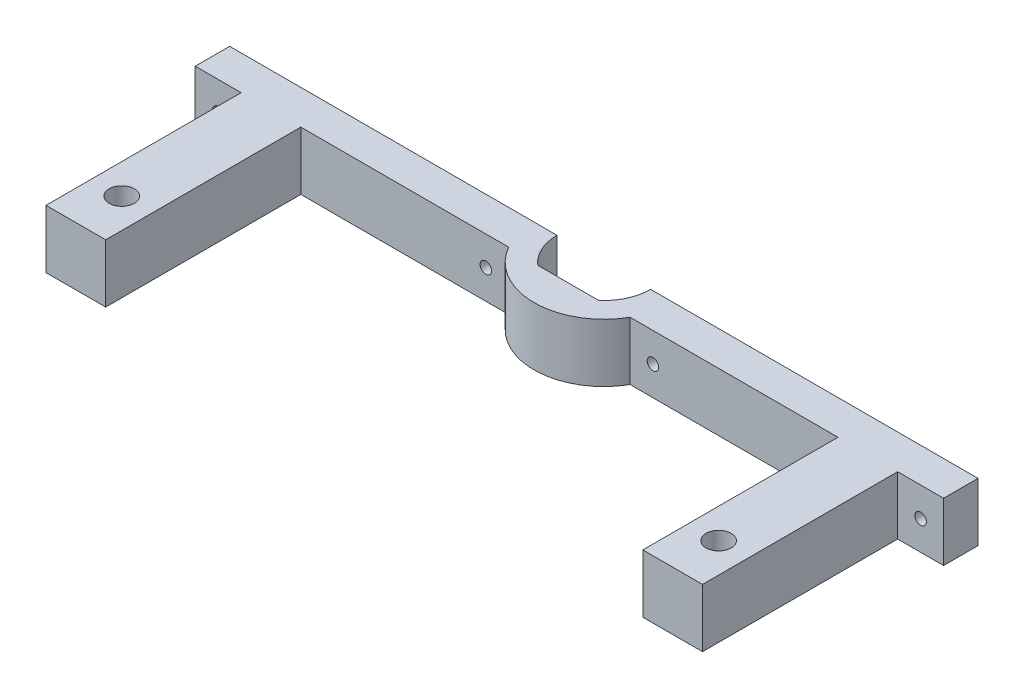
SolidWorks part; units mm, degrees
ref_plane "Front Plane" through (0, 0, 0) normal (0, 0, 1) x (1, 0, 0)
ref_plane "Top Plane" through (0, 0, 0) normal (0, 1, 0) x (1, 0, 0)
ref_plane "Right Plane" through (0, 0, 0) normal (1, 0, 0) x (0, 0, -1)
sketch "Sketch1" plane through (0, 0, 0) normal (0, 1, 0) x (1, 0, 0)
  line L1 (0, 0) -> (150, 0)
  line L2 (0, 0) -> (0, 100)
  line L3 (0, 100) -> (150, 100)
  line L4 (150, 0) -> (150, 100)
  dimension "D1" = 100
  dimension "D2" = 150
extrude "Boss-Extrude1" add sketch "Sketch1" along normal blind 12.7
sketch "Sketch2" plane through (0, 12.7, 0) normal (0, 1, 0) x (1, 0, 0)
  line L0 (75, 100) -> (75, 0) construction
  line L1 (150, 100) -> (0, 100) construction
  line L2 (0, 0) -> (150, 0) construction
  line L3 (0, 50) -> (150, 50) construction
  line L4 (0, 100) -> (0, 0) construction
  line L5 (150, 0) -> (150, 100) construction
  line L7 (85.2, 50) -> (64.8, 50)
  line L8 (85.2, 50) -> (85.2, 66.0625)
  line L9 (85.2, 66.0625) -> (64.8, 66.0625)
  line L10 (64.8, 50) -> (64.8, 66.0625)
  line L11 (68.3684, 57.75) -> (81.6316, 57.75)
  line L12 (68.3684, 57.75) -> (68.3684, 42.25)
  line L13 (68.3684, 42.25) -> (81.6316, 42.25)
  line L14 (81.6316, 57.75) -> (81.6316, 42.25)
  line L15 (68.3684, 57.75) -> (81.6316, 42.25) construction
  line L16 (68.3684, 42.25) -> (81.6316, 57.75) construction
  circle A0 centre (75, 50) radius 10.2
  circle A1 centre (10, 90) radius 2.75
  circle A2 centre (140, 90) radius 2.75
  circle A3 centre (140, 10) radius 2.75
  circle A4 centre (10, 10) radius 2.75
  point P22 (75, 42.25)
  dimension "D1" = 20.4
  dimension "D5" = 5.5
  dimension "D2" = 20.4
  dimension "D3" = 7.75
  dimension "D4" = 23.8125
  dimension "D6" = 10
  dimension "D7" = 10
extrude "Cut-Extrude1" cut sketch "Sketch2" against normal blind 12.7 contours L7 A0 L14 | L12 A0 L7 | L14 L11 L12 L7 | L14 A0 L7 | L7 A0 L12 | L14 L7 L12 L13 | A1 | A2 | A3 | A4
sketch "Sketch3" plane through (0, 12.7, 0) normal (0, 1, 0) x (1, 0, 0)
  line L0 (146.5, 50) -> (146.5, 42.5)
  line L1 (3.5, -30) -> (16.5, -30)
  line L2 (3.5, -30) -> (3.5, 50)
  line L3 (3.5, 50) -> (16.5, 50)
  line L4 (16.5, -30) -> (16.5, 50)
  line L5 (3.5, -30) -> (16.5, 50) construction
  line L6 (3.5, 50) -> (16.5, -30) construction
  line L7 (146.5, 50) -> (3.5, 50)
  line L8 (75, 50) -> (75, 42.5)
  line L9 (146.5, 42.5) -> (3.5, 42.5)
  line L10 (3.5, 50) -> (3.5, 42.5)
  line L11 (146.5, 50) -> (133.5, 50)
  line L12 (133.5, -30) -> (133.5, 50)
  line L13 (146.5, -30) -> (133.5, -30)
  line L14 (146.5, -30) -> (146.5, 50)
  circle A0 centre (75, 50) radius 15.2
  circle A1 centre (75, 50) radius 10.2
  point P4 (10, 10)
  circle M8 centre (10, 90) radius 2.75
  arc M10 (68.3684, 42.25) -> (68.3684, 57.75) centre (75, 50) cw
  line M11 (68.3684, 57.75) -> (81.6316, 57.75)
  arc M12 (81.6316, 57.75) -> (81.6316, 42.25) centre (75, 50) cw
  line M13 (0, 100) -> (0, 0)
  line M14 (0, 0) -> (150, 0)
  line M15 (150, 0) -> (150, 100)
  line M16 (150, 100) -> (0, 100)
  circle M17 centre (140, 90) radius 2.75
  dimension "D1" = 20.4
  dimension "D2" = 5
  dimension "D3" = 13
  dimension "D4" = 7.5
extrude "Cut-Extrude2" cut sketch "Sketch3" against normal blind 30 contours A0 L7 L0 L14 L2 L3 M14 M15 M16 M13 M8 M17 | A1 L7 A0 M12 M10 | L7 M12 M11 M10 | A0 L9 L4 L12 M14 | L9 L8 L7 M10 | L9 L7 L8 M12 | A1 M11
sketch "Sketch5" plane through (146.5, 0, 0) normal (1, 0, 0) x (0, 0, -1)
  line L0 (50, 12.7) -> (0, 12.7) construction
  line L1 (50, 0) -> (42.5, 0)
  line L2 (50, 0) -> (50, 12.7)
  line L3 (50, 12.7) -> (42.5, 12.7)
  line L4 (42.5, 0) -> (42.5, 12.7)
  dimension "D1" = 7.5
extrude "Boss-Extrude2" add sketch "Sketch5" along normal blind 10
sketch "Sketch6" plane through (3.5, 0, 0) normal (-1, 0, 0) x (0, 0, 1)
  line L0 (0, 12.7) -> (-50, 12.7) construction
  line L1 (-50, 0) -> (-42.5, 0)
  line L2 (-50, 0) -> (-50, 12.7)
  line L3 (-50, 12.7) -> (-42.5, 12.7)
  line L4 (-42.5, 0) -> (-42.5, 12.7)
  dimension "D1" = 7.5
extrude "Boss-Extrude3" add sketch "Sketch6" along normal blind 10
sketch "Sketch4" plane through (0, 0, -50) normal (0, 0, -1) x (-1, 0, 0)
  line L0 (-85.2, 0) -> (-85.2, 12.7) construction
  line L5 (-156.5, 12.7) -> (-85.2, 12.7) construction
  line L6 (-156.5, 0) -> (-146.5, 0)
  line L7 (-75, 6.35) -> (-75, 11.35) construction
  line L9 (-156.5, 0) -> (-156.5, 12.7)
  line L10 (-156.5, 12.7) -> (-146.5, 12.7)
  line L11 (-146.5, 0) -> (-146.5, 12.7)
  line L12 (-85.2, 0) -> (-156.5, 0) construction
  line L13 (-146.5, 12.7) -> (-133.5, 12.7)
  line L14 (-146.5, 12.7) -> (-146.5, 0)
  line L15 (-146.5, 0) -> (-133.5, 0)
  line L16 (-133.5, 12.7) -> (-133.5, 0)
  line L17 (-156.5, 6.35) -> (6.5, 6.35) construction
  line L18 (6.5, 12.7) -> (6.5, 0) construction
  circle A0 centre (-151.5, 6.35) radius 1.25
  circle A1 centre (-140, 6.35) radius 2.5
  circle A2 centre (-93.2, 6.35) radius 1.25
  circle A3 centre (-56.8, 6.35) radius 1.25
  circle A4 centre (-10, 6.35) radius 2.5
  circle A5 centre (1.5, 6.35) radius 1.25
  point P4 (-75, 6.35)
  dimension "D2" = 13
  dimension "D3" = 2.5
  dimension "D5" = 5
  dimension "D7" = 2.5
  dimension "D1" = 10
  dimension "D4" = 5
  dimension "D6" = 6.5
  dimension "D8" = 8
  dimension "D9" = 5
extrude "Cut-Extrude3" cut sketch "Sketch4" against normal blind 40 contours A0 | A2 | A3 | A5
